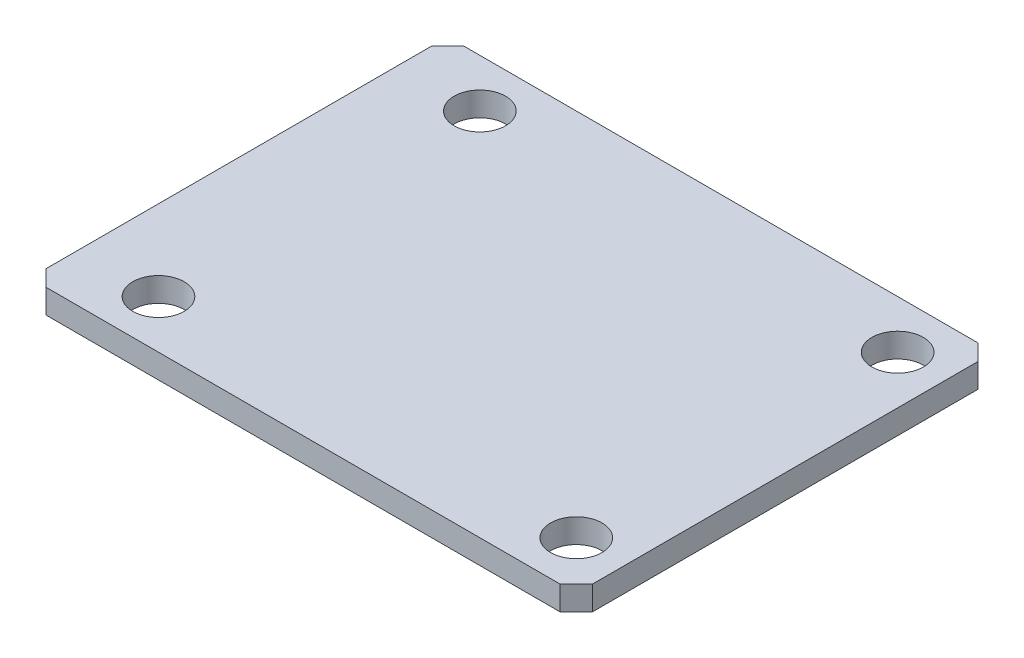
SolidWorks part; units mm, degrees
ref_plane "前视基准面" through (0, 0, 0) normal (0, 0, 1) x (1, 0, 0)
ref_plane "上视基准面" through (0, 0, 0) normal (0, 1, 0) x (1, 0, 0)
ref_plane "右视基准面" through (0, 0, 0) normal (1, 0, 0) x (0, 0, -1)
other "Configuration Table"
sketch "草图1" plane through (0, 0, 0) normal (0, 1, 0) x (1, 0, 0)
  line L0 (-17, 12) -> (-16, 13)
  line L1 (-16, -13) -> (16, -13)
  line L2 (-17, -12) -> (-17, 12)
  line L3 (-16, 13) -> (16, 13)
  line L4 (17, -12) -> (17, 12)
  line L5 (-17, -13) -> (17, 13) construction
  line L6 (-17, 13) -> (17, -13) construction
  line L7 (16, 13) -> (17, 12)
  line L8 (16, -13) -> (17, -12)
  line L9 (-17, -12) -> (-16, -13)
  point P0 (0, 0)
  dimension "D1" = 34
  dimension "D2" = 26
extrude "凸台-拉伸1" add sketch "草图1" along normal blind 1.5
sketch "草图2" plane through (0, 1.5, 0) normal (0, 1, 0) x (1, 0, 0)
  line L0 (17, -12) -> (17, 12) construction
  line L2 (16, 13) -> (-16, 13) construction
  circle A0 centre (14, 10) radius 1.6
  circle A1 centre (14, -10) radius 1.6
  circle A2 centre (-12, 10) radius 1.6
  circle A3 centre (-12, -10) radius 1.6
  dimension "D1" = 3.2
  dimension "D3" = 3
  dimension "D4" = 3.2
  dimension "D5" = 20
  dimension "D6" = 3.2
  dimension "D7" = 26
  dimension "D8" = 3.2
  dimension "D2" = 3
extrude "切除-拉伸1" cut sketch "草图2" against normal blind 1.5
